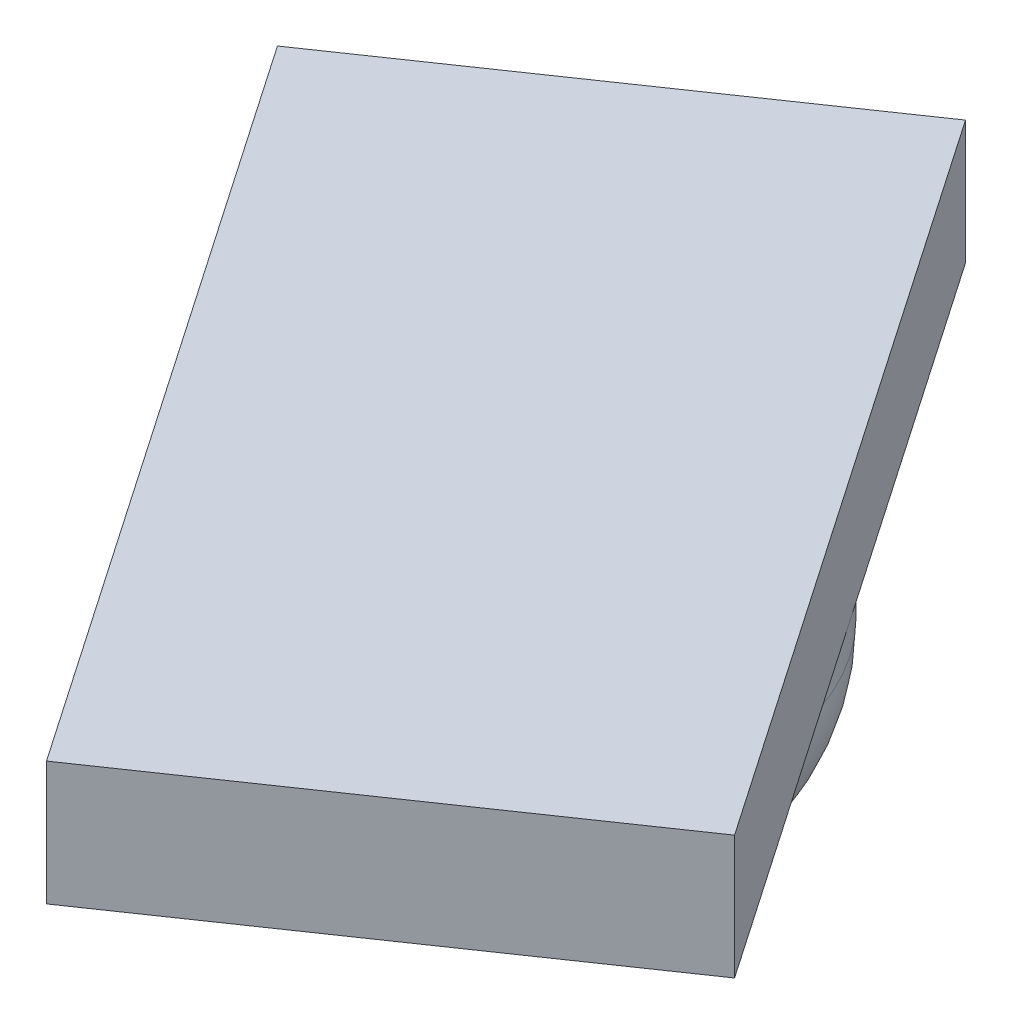
SolidWorks part; units mm, degrees
ref_plane "Front Plane" through (0, 0, 0) normal (0, 0, 1) x (1, 0, 0)
ref_plane "Top Plane" through (0, 0, 0) normal (0, 1, 0) x (1, 0, 0)
ref_plane "Right Plane" through (0, 0, 0) normal (1, 0, 0) x (0, 0, -1)
sketch "Sketch1" plane through (0, 0, 0) normal (0, 1, 0) x (1, 0, 0)
  circle A1 centre (0, 0) radius 4
extrude "Boss-Extrude1" add sketch "Sketch1" along normal blind 5.5
sketch "Sketch2" plane through (0, 5.5, 0) normal (0, 1, 0) x (1, 0, 0)
  line L0 (0.7726, -8.2002) -> (7.3706, -3.6762)
  line L1 (0.7726, -8.2002) -> (-7.3706, 3.6762)
  line L2 (7.3706, -3.6762) -> (-0.7726, 8.2002)
  line L3 (-7.3706, 3.6762) -> (-0.7726, 8.2002)
  line L4 (0.7726, -8.2002) -> (-0.7726, 8.2002) construction
  line L5 (7.3706, -3.6762) -> (-7.3706, 3.6762) construction
  point P1 (0, 0)
  dimension "D1" = 14.4
  dimension "D2" = 8
extrude "Boss-Extrude2" add sketch "Sketch2" against normal blind 2
fillet "Fillet3" radius 3 1 edges at (0, 0, 4)
sketch "Sketch3" plane through (4.0716, 0, 5.9382) normal (0.5655, 0, 0.8247) x (0.8247, 0, -0.5655)
  line L0 (-4, 5.5) -> (4, 5.5) construction
  line L2 (0, 5.5) -> (-4, 5.5)
  line L3 (0, 5.5) -> (0, 3.5)
  line L4 (0, 3.5) -> (-4, 3.5)
  line L5 (-4, 5.5) -> (-4, 3.5)
